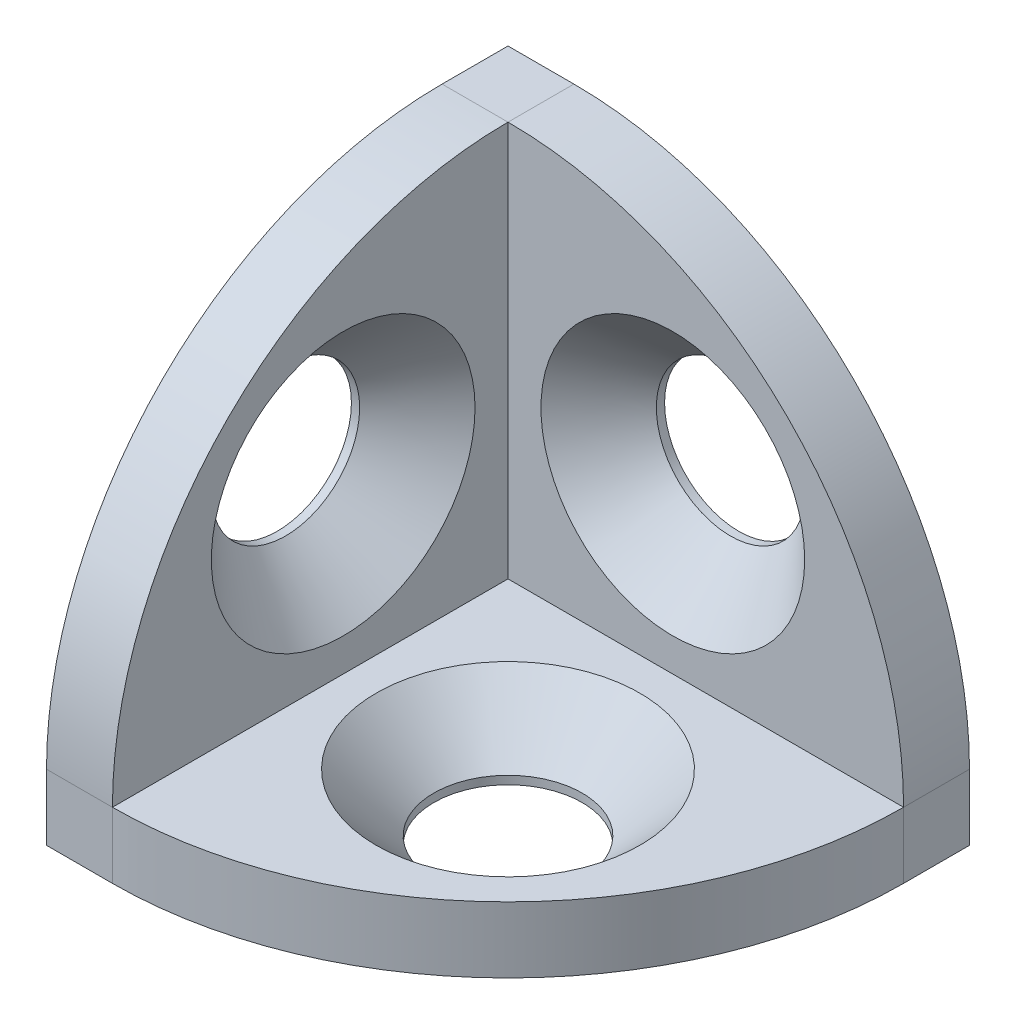
SolidWorks part; units mm, degrees
material "Алюминиевый сплав"
ref_plane "Спереди" through (0, 0, 0) normal (0, 0, 1) x (1, 0, 0)
ref_plane "Сверху" through (0, 0, 0) normal (0, 1, 0) x (1, 0, 0)
ref_plane "Справа" through (0, 0, 0) normal (1, 0, 0) x (0, 0, -1)
sketch "Эскиз1" plane through (0, 0, 0) normal (0, 0, 1) x (1, 0, 0)
  line L0 (0, 0) -> (0, 28)
  line L1 (0, 28) -> (4, 28)
  line L2 (28, 4) -> (28, 0)
  line L3 (28, 0) -> (0, 0)
  arc A0 (4, 28) -> (28, 4) centre (4, 4) cw
  dimension "D1" = 28
  dimension "D2" = 4
extrude "Бобышка-Вытянуть1" add sketch "Эскиз1" along normal blind 4
hole_wizard "Зенковка для винта с полупотайной головкой M81" positions "Эскиз2" profile "Эскиз3" countersink size "M8" standard "ISO"
sketch "Эскиз2" plane through (0, 0, 4) normal (0, 0, 1) x (1, 0, 0)
  line L0 (0, 0) -> (28, 0) construction
  line L1 (14, 14) -> (0, 14)
  line L2 (0, 28) -> (0, 0) construction
  line L4 (14, 14) -> (14, 0)
  point P0 (14, 14)
  dimension "D1" = 14
sketch "Эскиз3" plane through (14, 14, 4) normal (1, 0, 0) x (0, -1, 0)
  line L0 (0, 0) -> (0, 11.9539)
  line L1 (0, 11.9539) -> (4.5, 9.25)
  line L2 (4.5, 9.25) -> (4.5, 3.5)
  line L3 (4.5, 3.5) -> (8, 0)
  line L5 (8, 0) -> (0, 0)
  line L6 (-4.5, 3.5) -> (-8, 0) construction
  line L10 (0, 11.9539) -> (-4.5, 9.25) construction
  line L11 (0, -6.35) -> (0, 107.95) construction
  dimension "Диаметр отверстия" = 9
  dimension "Глубина отверстия" = 9.25
  dimension "Диаметр передней зенковки" = 16
  dimension "Угол передней зенковки" = 90
  dimension "Угол заточки сверла" = 118
sketch "Эскиз4" plane through (0, 0, 0) normal (0, 0, -1) x (-1, 0, 0)
  line L0 (-14, 14) -> (-14, 3) construction
  line L1 (-3, 18) -> (-1.5, 18)
  line L2 (-3, 18) -> (-3, 10)
  line L3 (-3, 10) -> (-1.5, 10)
  line L4 (-1.5, 18) -> (-1.5, 10)
  line L5 (-18, 3) -> (-10, 3)
  line L6 (-18, 3) -> (-18, 1.5)
  line L7 (-18, 1.5) -> (-10, 1.5)
  line L8 (-10, 3) -> (-10, 1.5)
  line L9 (-14, 14) -> (-3, 14) construction
  line L10 (0, 28) -> (0, 0) construction
  point P12 (-10.346, 4.0183)
  point P15 (-14, 3.543)
  dimension "D1" = 1.5
  dimension "D2" = 1.5
  dimension "D3" = 8
extrude "Бобышка-Вытянуть2" add sketch "Эскиз4" along normal blind 1
ref_plane "Плоскость1" through (0, 0, 0) normal (0, -0.7071, 0.7071) x (1, 0, 0)
ref_plane "Плоскость2" through (0, 0, 0) normal (-0.7071, 0, 0.7071) x (0.7071, 0, 0.7071)
mirror "Зеркальное отражение1" about plane through (0, 0, 0) normal (0, -0.7071, 0.7071) of "Бобышка-Вытянуть2", "Бобышка-Вытянуть1", "Зенковка для винта с полупотайной головкой M81"
mirror "Зеркальное отражение2" about plane through (0, 0, 0) normal (-0.7071, 0, 0.7071) of "Зеркальное отражение1", "Бобышка-Вытянуть1", "Зенковка для винта с полупотайной головкой M81", "Бобышка-Вытянуть2"
